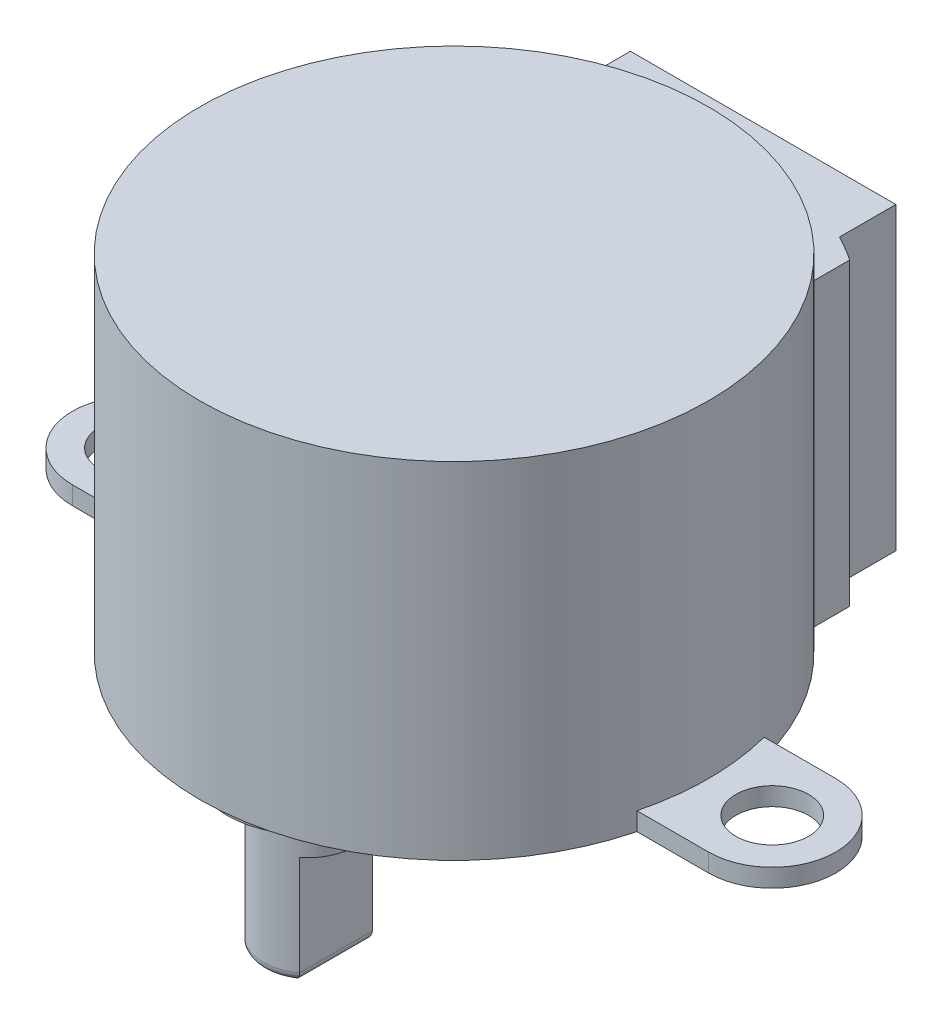
SolidWorks part; units mm, degrees
ref_plane "Front" through (0, 0, 0) normal (0, 0, 1) x (1, 0, 0)
ref_plane "Top" through (0, 0, 0) normal (0, 1, 0) x (1, 0, 0)
ref_plane "Right" through (0, 0, 0) normal (1, 0, 0) x (0, 0, -1)
sketch "Sketch1" plane through (0, 0, 0) normal (0, 1, 0) x (1, 0, 0)
  circle A0 centre (0, 0) radius 14
  dimension "D1" = 28
extrude "Boss-Extrude1" add sketch "Sketch1" along normal blind 19
sketch "Sketch2" plane through (0, 0, 0) normal (0, 1, 0) x (1, 0, 0)
  line L0 (0, 0) -> (0, 17) construction
  line L1 (7.3, 17) -> (-7.3, 17)
  line L2 (7.3, 17) -> (7.3, 13.9022)
  line L3 (-7.3, 17) -> (-7.3, 13.9022)
  line L4 (-8.675, 10.9884) -> (-8.675, 13.0884)
  line L5 (8.675, 10.9884) -> (8.675, 13.0884)
  circle A0 centre (0, 0) radius 14 construction
  arc A1 (8.675, 10.9884) -> (-8.675, 10.9884) centre (0, 0) ccw
  arc A2 (-8.675, 13.0884) -> (-7.3, 13.9022) centre (0, 0) cw
  arc A3 (8.675, 13.0884) -> (7.3, 13.9022) centre (0, 0) ccw
  point P6 (0, 17)
  point P7 (8.5836, 11.0599)
  point P16 (-8.5738, 10.9487)
  dimension "D3" = 2.1
  dimension "D4" = 17.35
  dimension "D1" = 14.6
  dimension "D2" = 17
extrude "Boss-Extrude2" add sketch "Sketch2" along normal blind 16.5
sketch "Sketch3" plane through (0, 0, 0) normal (0, 1, 0) x (1, 0, 0)
  line L0 (-17.5, 0) -> (17.5, 0) construction
  line L1 (-17.5, 3.5) -> (-13.5554, 3.5)
  line L2 (-17.5, -3.5) -> (-13.5554, -3.5)
  line L3 (17.5, 3.5) -> (13.5554, 3.5)
  line L4 (17.5, -3.5) -> (13.5554, -3.5)
  circle A0 centre (-17.5, 0) radius 2
  circle A1 centre (17.5, 0) radius 2
  arc A2 (-17.5, 3.5) -> (-17.5, -3.5) centre (-17.5, 0) ccw
  arc A3 (17.5, 3.5) -> (17.5, -3.5) centre (17.5, 0) cw
  arc A4 (-8.675, 10.9884) -> (8.675, 10.9884) centre (0, 0) ccw construction
  arc A5 (13.5554, 3.5) -> (13.5554, -3.5) centre (0, 0) cw
  arc A6 (-13.5554, 3.5) -> (-13.5554, -3.5) centre (0, 0) ccw
  point P4 (0, 0)
  dimension "D2" = 4
  dimension "D3" = 3.5
  dimension "D1" = 35
extrude "Boss-Extrude3" add sketch "Sketch3" along normal blind 1
sketch "Sketch4" plane through (0, 0, 0) normal (0, -1, 0) x (1, 0, 0)
  line L0 (0, 0) -> (0, 8) construction
  circle A0 centre (0, 8) radius 4.5
  dimension "D1" = 9
  dimension "D2" = 8
extrude "Boss-Extrude4" add sketch "Sketch4" along normal blind 1.5
sketch "Sketch5" plane through (0, -1.5, 0) normal (0, -1, 0) x (1, 0, 0)
  circle A0 centre (0, 8) radius 2.5
  circle A1 centre (0, 8) radius 4.5
  circle A2 centre (0, 8) radius 4.5 construction
  dimension "D2" = 5
  dimension "D1" = 0
extrude "Boss-Extrude5" add sketch "Sketch5" along normal blind 2.5 contours A0
sketch "Sketch6" plane through (0, -4, 0) normal (0, -1, 0) x (1, 0, 0)
  line L0 (-1.5, 8) -> (1.5, 8) construction
  line L1 (-1.5, 10) -> (-1.5, 6)
  line L2 (1.5, 10) -> (1.5, 6)
  circle A0 centre (0, 8) radius 2.5 construction
  circle A1 centre (0, 8) radius 2.5
  circle A2 centre (0, 8) radius 2.5 construction
  circle A3 centre (0, 8) radius 2.5 construction
  arc A4 (-1.5, 10) -> (1.5, 10) centre (0, 8) cw
  arc A5 (-1.5, 6) -> (1.5, 6) centre (0, 8) ccw
  dimension "D2" = 3
  dimension "D1" = 0
extrude "Boss-Extrude6" add sketch "Sketch6" along normal blind 6
fillet "Fillet1" radius 0.5 4 edges at (1.5, -10, 8) (0, -10, 10.5) (0, -10, 5.5) (-1.5, -10, 8)
sketch "Sketch7" plane through (0, -10, 0) normal (0, -1, 0) x (1, 0, 0)
  line L0 (-1, 8) -> (1, 8) construction
  line L1 (-1, 9.7321) -> (-1, 6.2679) construction
  line L2 (1, 6.2679) -> (1, 9.7321) construction
  circle A1 centre (0, 8) radius 0.5
  dimension "D1" = 1
extrude "Cut-Extrude1" cut sketch "Sketch7" against normal blind 1 contours A1
